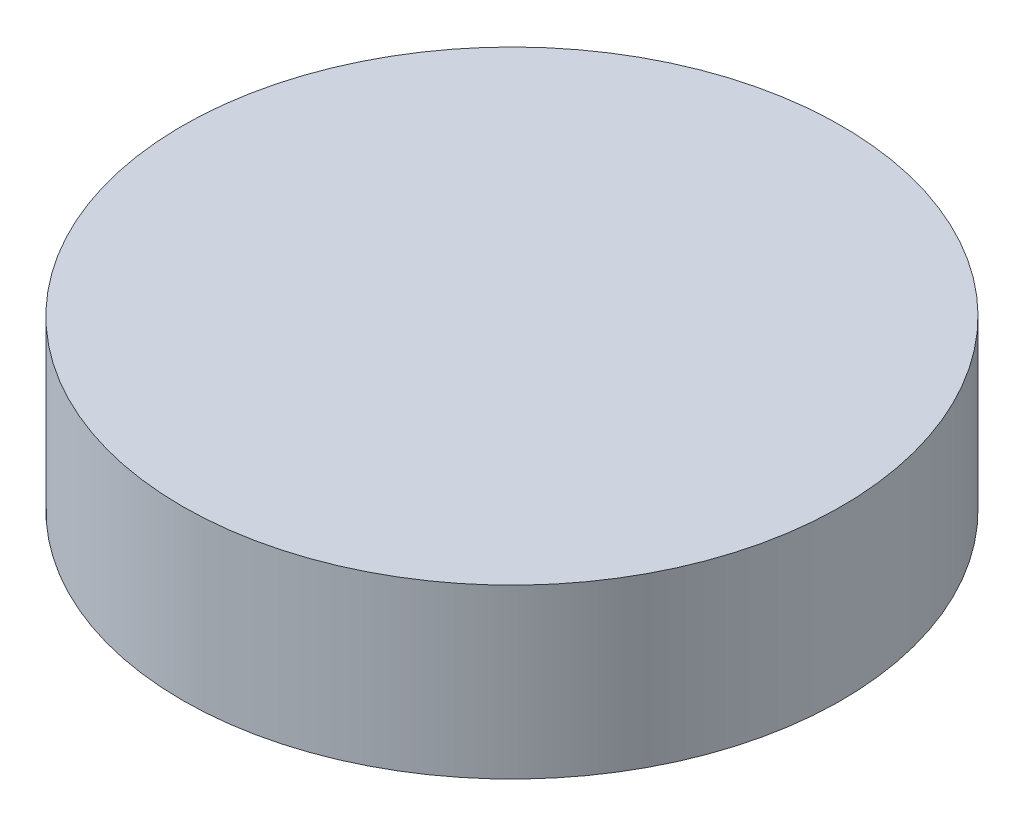
SolidWorks part; units mm, degrees
ref_plane "Front Plane" through (0, 0, 0) normal (0, 0, 1) x (1, 0, 0)
ref_plane "Top Plane" through (0, 0, 0) normal (0, 1, 0) x (1, 0, 0)
ref_plane "Right Plane" through (0, 0, 0) normal (1, 0, 0) x (0, 0, -1)
sketch "Sketch1" plane through (0, 0, 0) normal (0, 1, 0) x (1, 0, 0)
  circle A0 centre (0, 0) radius 1.9939
  dimension "D1" = 3.9878
extrude "Boss-Extrude1" add sketch "Sketch1" along normal blind 1.016
